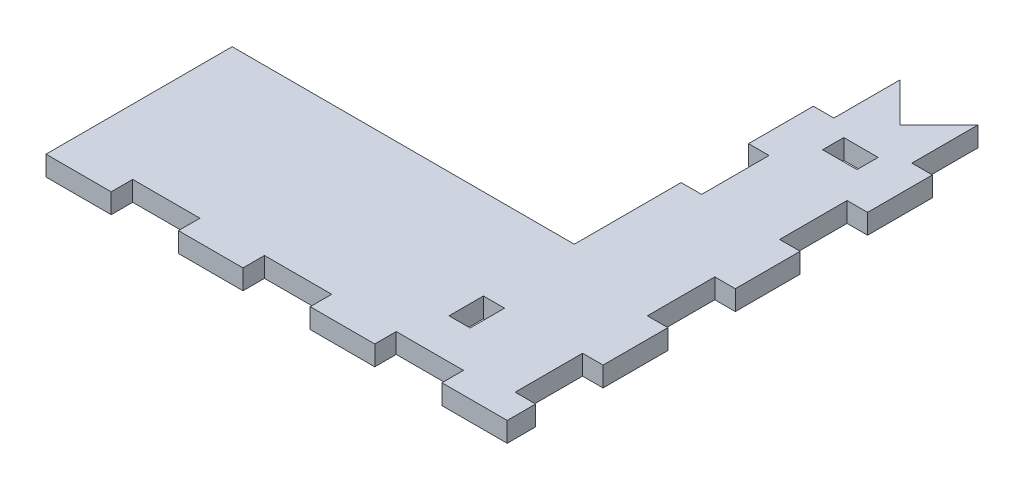
SolidWorks part; units mm, degrees
ref_plane "Front Plane" through (0, 0, 0) normal (0, 0, 1) x (1, 0, 0)
ref_plane "Top Plane" through (0, 0, 0) normal (0, 1, 0) x (1, 0, 0)
ref_plane "Right Plane" through (0, 0, 0) normal (1, 0, 0) x (0, 0, -1)
sketch "Sketch1" plane through (0, 0, 0) normal (0, 1, 0) x (1, 0, 0)
  line L0 (0, 0) -> (0, 75) construction
  line L1 (-34.8722, 75) -> (34.8722, 75) construction
  line L2 (-34.8722, 75) -> (-34.8722, 0) construction
  line L3 (-34.8722, 0) -> (34.8722, 0)
  line L4 (34.8722, 75) -> (34.8722, 0)
  line L5 (34.8722, 0) -> (34.8722, 75) construction
  line L6 (34.8722, 75) -> (16.8722, 75)
  line L7 (16.8722, 75) -> (16.8722, 28.75)
  line L8 (16.8722, 28.75) -> (-34.8722, 28.75)
  line L9 (-34.8722, 28.75) -> (-34.8722, 0)
  line L10 (24.9087, 3.75) -> (24.9087, 10.75) construction
  line L12 (19.8722, 75) -> (19.8722, 0) construction
  line L13 (31.8722, 75) -> (31.8722, 0) construction
  line L14 (31.8722, 37.5) -> (34.8722, 37.5) construction
  line L15 (19.8722, 37.5) -> (16.8722, 37.5) construction
  line L16 (31.8722, 75) -> (25.8722, 69) construction
  line L17 (25.8722, 69) -> (19.8722, 75) construction
  line L18 (25.8722, 75) -> (25.8722, 69) construction
  line L19 (25.8722, 69) -> (31.8722, 69) construction
  line L20 (34.8722, 60) -> (16.8722, 60) construction
  line L21 (16.8722, 63) -> (34.8722, 63) construction
  line L22 (25.8722, 63) -> (25.8722, 60) construction
  line L23 (-34.8722, 3) -> (34.8722, 3) construction
  line L24 (-34.8722, 0) -> (-34.8722, -0.75) construction
  line L25 (-34.8722, -0.75) -> (34.8722, -0.75) construction
  line L26 (34.8722, -0.75) -> (34.8722, 0) construction
  line L27 (-3, 0) -> (-3, 3) construction
  line L28 (-3, 1.5) -> (0, 1.5) construction
  line L29 (-34.8722, 3.75) -> (34.8722, 3.75) construction
  line L30 (-3, 3) -> (-3, 3.75) construction
  line L31 (-3, 0) -> (-3, -0.75) construction
  line L34 (-24.9087, 0) -> (-24.9087, 3.75) construction
  line L39 (-14.9452, 0) -> (-14.9452, 3.75) construction
  line L40 (-4.9817, 0) -> (-4.9817, 3.75) construction
  line L41 (4.9817, 0) -> (4.9817, 3.75) construction
  line L42 (14.9452, 0) -> (14.9452, 3.75) construction
  line L43 (24.9087, 0) -> (24.9087, 3.75) construction
  line L44 (34.8722, 0.5) -> (-34.8722, 0.5) construction
  line L45 (24.9087, 10.75) -> (-24.9087, 10.75) construction
  line L46 (-24.9087, 10.75) -> (-24.9087, 3.75) construction
  line L47 (16.8722, 28.75) -> (16.8722, 10.75) construction
  line L48 (16.8722, 28.75) -> (34.8722, 28.75) construction
  dimension "D1" = 12
  dimension "D2" = 0.75
  dimension "D3" = 0.5
  dimension "D4" = 7
extrude "Boss-Extrude1" add sketch "Sketch1" against normal up to vertex (3 mm away)
sketch "Sketch2" plane through (0, 0, 0) normal (0, 1, 0) x (1, 0, 0)
  line L0 (-34.8722, 0) -> (34.8722, 0) construction
  line L2 (28.3722, 60) -> (23.3722, 60)
  line L3 (34.8722, 75) -> (34.8722, 0) construction
  line L4 (34.8722, 75) -> (16.8722, 75) construction
  line L5 (16.8722, 75) -> (16.8722, 28.75) construction
  line L6 (16.8722, 28.75) -> (-34.8722, 28.75) construction
  line L7 (-34.8722, 28.75) -> (-34.8722, 0) construction
  line L8 (-34.8722, 0) -> (34.8722, 0)
  line L9 (34.8722, 75) -> (34.8722, 0) construction
  line L10 (34.8722, 75) -> (16.8722, 75) construction
  line L11 (16.8722, 75) -> (16.8722, 28.75) construction
  line L12 (16.8722, 28.75) -> (-34.8722, 28.75) construction
  line L13 (-34.8722, 28.75) -> (-34.8722, 0) construction
  line L14 (31.8722, 75) -> (31.8722, 0) construction
  line L15 (19.8722, 0) -> (19.8722, 75) construction
  line L16 (34.8722, 3.75) -> (-34.8722, 3.75) construction
  line L17 (34.8722, 60) -> (16.8722, 60) construction
  line L18 (34.8722, 63) -> (16.8722, 63) construction
  line L19 (16.8722, 63) -> (34.8722, 63) construction
  line L20 (34.8722, 60) -> (16.8722, 60) construction
  line L21 (31.8722, 75) -> (31.8722, 0) construction
  line L22 (-34.8722, 3.75) -> (34.8722, 3.75) construction
  line L23 (25.8722, 60) -> (25.8722, 3.75) construction
  line L24 (34.8722, 0) -> (34.8722, 0.5)
  line L25 (25.8722, 60) -> (25.8722, 63) construction
  line L26 (28.3722, 60) -> (28.3722, 63)
  line L27 (28.3722, 63) -> (23.3722, 63)
  line L28 (23.3722, 60) -> (23.3722, 63)
  line L29 (31.8722, 65) -> (34.8722, 65)
  line L30 (33.3722, 65) -> (33.3722, 75) construction
  line L31 (33.3722, 65) -> (33.3722, 55) construction
  line L32 (34.8722, 55) -> (31.8722, 55)
  line L33 (31.8722, 45) -> (34.8722, 45)
  line L34 (33.3722, 55) -> (33.3722, 45) construction
  line L37 (33.3722, 45) -> (33.3722, 35) construction
  line L38 (34.8722, 35) -> (31.8722, 35)
  line L39 (34.8722, 25) -> (31.8722, 25)
  line L40 (33.3722, 25) -> (33.3722, 35) construction
  line L41 (34.8722, 15) -> (31.8722, 15)
  line L42 (34.8722, 5) -> (31.8722, 5)
  line L43 (33.3722, 5) -> (33.3722, 15) construction
  line L44 (33.3722, 15) -> (33.3722, 25) construction
  line L47 (34.8722, 0.5) -> (24.9087, 0.5)
  line L48 (0, 0) -> (0, 75) construction
  line L49 (0, 0) -> (0, 75) construction
  line L54 (24.9087, 0) -> (24.9087, 3.75) construction
  line L55 (24.9087, 0.5) -> (24.9087, 3.75)
  line L108 (31.8722, 25) -> (31.8722, 35)
  line L109 (34.8722, 25) -> (34.8722, 35)
  line L110 (31.8722, 45) -> (31.8722, 55)
  line L111 (34.8722, 55) -> (34.8722, 45)
  line L112 (34.8722, 65) -> (34.8722, 75)
  line L113 (34.8722, 75) -> (31.8722, 75)
  line L114 (31.8722, 75) -> (31.8722, 65)
  line L115 (16.8722, 25) -> (19.8722, 25) construction
  line L116 (16.8722, 25) -> (16.8722, 35) construction
  line L117 (16.8722, 35) -> (19.8722, 35) construction
  line L118 (19.8722, 25) -> (19.8722, 35) construction
  line L119 (19.8722, 45) -> (16.8722, 45)
  line L120 (16.8722, 55) -> (16.8722, 45)
  line L121 (16.8722, 55) -> (19.8722, 55)
  line L122 (19.8722, 45) -> (19.8722, 55)
  line L123 (16.8722, 75) -> (19.8722, 75)
  line L124 (16.8722, 65) -> (16.8722, 75)
  line L125 (19.8722, 65) -> (16.8722, 65)
  line L126 (19.8722, 75) -> (19.8722, 65)
  line L133 (31.8722, 5) -> (31.8722, 15)
  line L134 (34.8722, 15) -> (34.8722, 5)
  line L135 (24.9087, 3.75) -> (14.9452, 3.75)
  line L136 (14.9452, 3.75) -> (14.9452, 0.5)
  line L137 (14.9452, 0.5) -> (4.9817, 0.5)
  line L138 (4.9817, 0.5) -> (4.9817, 3.75)
  line L139 (4.9817, 3.75) -> (-4.9817, 3.75)
  line L140 (-4.9817, 3.75) -> (-4.9817, 0.5)
  line L141 (-4.9817, 0.5) -> (-14.9452, 0.5)
  line L142 (-14.9452, 0.5) -> (-14.9452, 3.75)
  line L143 (-14.9452, 3.75) -> (-24.9087, 3.75)
  line L144 (-24.9087, 3.75) -> (-24.9087, 0.5)
  line L145 (-24.9087, 0.5) -> (-34.8722, 0.5)
  line L146 (-34.8722, 0.5) -> (-34.8722, 0)
  line L147 (-14.9452, 0) -> (-14.9452, 3.75) construction
  line L148 (34.8722, 0.5) -> (-34.8722, 0.5) construction
  line L149 (4.9817, 0) -> (4.9817, 3.75) construction
  line L150 (14.9452, 0) -> (14.9452, 3.75) construction
  line L152 (19.8722, 15) -> (16.8722, 15)
  line L153 (19.8722, 15) -> (19.8722, 10)
  line L154 (19.8722, 10) -> (16.8722, 10)
  line L155 (16.8722, 15) -> (16.8722, 10)
  dimension "D1" = 5
  dimension "D2" = 10
  dimension "D3" = 5
sketch "Sketch8" plane through (0, 0, 0) normal (0, 1, 0) x (1, 0, 0)
  line L45 (34.9722, 55.1) -> (31.7722, 55.1)
  line L46 (31.7722, 55.1) -> (31.7722, 44.9)
  line L47 (31.7722, 44.9) -> (34.9722, 44.9)
  line L48 (34.9722, 44.9) -> (34.9722, 55.1)
  line L49 (34.8722, 55) -> (31.8722, 55)
  line L50 (31.8722, 55) -> (31.8722, 45)
  line L51 (31.8722, 45) -> (34.8722, 45)
  line L52 (34.8722, 45) -> (34.8722, 55)
  line L53 (34.8722, 55) -> (31.8722, 55) construction
  line L54 (31.8722, 55) -> (31.8722, 45) construction
  line L55 (31.8722, 45) -> (34.8722, 45) construction
  line L56 (34.8722, 45) -> (34.8722, 55) construction
  line L57 (31.8722, 65) -> (34.8722, 65)
  line L58 (34.8722, 65) -> (34.8722, 75)
  line L59 (34.8722, 75) -> (31.8722, 75)
  line L60 (31.8722, 75) -> (31.8722, 65)
  line L61 (31.8722, 65) -> (34.8722, 65) construction
  line L62 (34.8722, 65) -> (34.8722, 75) construction
  line L63 (34.8722, 75) -> (31.8722, 75) construction
  line L64 (31.8722, 75) -> (31.8722, 65) construction
  line L65 (23.3722, 60) -> (28.3722, 60)
  line L66 (28.3722, 60) -> (28.3722, 63)
  line L67 (28.3722, 63) -> (23.3722, 63)
  line L68 (23.3722, 63) -> (23.3722, 60)
  line L69 (23.3722, 60) -> (28.3722, 60) construction
  line L70 (28.3722, 60) -> (28.3722, 63) construction
  line L71 (28.3722, 63) -> (23.3722, 63) construction
  line L72 (23.3722, 63) -> (23.3722, 60) construction
  line L73 (34.8722, 15) -> (31.8722, 15)
  line L74 (31.8722, 15) -> (31.8722, 5)
  line L75 (31.8722, 5) -> (34.8722, 5)
  line L76 (34.8722, 5) -> (34.8722, 15)
  line L77 (34.8722, 15) -> (31.8722, 15) construction
  line L78 (31.8722, 15) -> (31.8722, 5) construction
  line L79 (31.8722, 5) -> (34.8722, 5) construction
  line L80 (34.8722, 5) -> (34.8722, 15) construction
  line L81 (31.8722, 35) -> (31.8722, 25)
  line L82 (31.8722, 25) -> (34.8722, 25)
  line L83 (34.8722, 25) -> (34.8722, 35)
  line L84 (34.8722, 35) -> (31.8722, 35)
  line L85 (31.8722, 35) -> (31.8722, 25) construction
  line L86 (31.8722, 25) -> (34.8722, 25) construction
  line L87 (34.8722, 25) -> (34.8722, 35) construction
  line L88 (34.8722, 35) -> (31.8722, 35) construction
  line L89 (19.8722, 15) -> (16.8722, 15) construction
  line L90 (16.8722, 15) -> (16.8722, 10) construction
  line L91 (19.8722, 10) -> (16.8722, 10) construction
  line L92 (19.8722, 15) -> (19.8722, 10) construction
  line L93 (19.8722, 15) -> (16.8722, 15) construction
  line L94 (16.8722, 15) -> (16.8722, 10) construction
  line L95 (19.8722, 10) -> (16.8722, 10) construction
  line L96 (19.8722, 15) -> (19.8722, 10) construction
  line L97 (16.8722, 65) -> (19.8722, 65)
  line L98 (19.8722, 65) -> (19.8722, 75)
  line L99 (19.8722, 75) -> (16.8722, 75)
  line L100 (16.8722, 75) -> (16.8722, 65)
  line L101 (16.8722, 65) -> (19.8722, 65) construction
  line L102 (19.8722, 65) -> (19.8722, 75) construction
  line L103 (19.8722, 75) -> (16.8722, 75) construction
  line L104 (16.8722, 75) -> (16.8722, 65) construction
  line L105 (16.8722, 55) -> (16.8722, 45)
  line L106 (19.8722, 55) -> (16.8722, 55)
  line L107 (19.8722, 45) -> (19.8722, 55)
  line L108 (16.8722, 45) -> (19.8722, 45)
  line L109 (-34.8722, 0.5) -> (-34.8722, 0)
  line L110 (-34.8722, 0) -> (34.8722, 0)
  line L111 (34.8722, 0) -> (34.8722, 0.5)
  line L112 (34.8722, 0.5) -> (24.9087, 0.5)
  line L113 (24.9087, 0.5) -> (24.9087, 3.75)
  line L114 (24.9087, 3.75) -> (14.9452, 3.75)
  line L115 (14.9452, 3.75) -> (14.9452, 0.5)
  line L116 (14.9452, 0.5) -> (4.9817, 0.5)
  line L117 (4.9817, 0.5) -> (4.9817, 3.75)
  line L118 (4.9817, 3.75) -> (-4.9817, 3.75)
  line L119 (-4.9817, 3.75) -> (-4.9817, 0.5)
  line L120 (-4.9817, 0.5) -> (-14.9452, 0.5)
  line L121 (-14.9452, 0.5) -> (-14.9452, 3.75)
  line L122 (-14.9452, 3.75) -> (-24.9087, 3.75)
  line L123 (-24.9087, 3.75) -> (-24.9087, 0.5)
  line L124 (-24.9087, 0.5) -> (-34.8722, 0.5)
  line L125 (-34.8722, 0.5) -> (-34.8722, 0) construction
  line L126 (-34.8722, 0) -> (34.8722, 0) construction
  line L127 (34.8722, 0) -> (34.8722, 0.5) construction
  line L128 (34.8722, 0.5) -> (24.9087, 0.5) construction
  line L129 (24.9087, 0.5) -> (24.9087, 3.75) construction
  line L130 (24.9087, 3.75) -> (14.9452, 3.75) construction
  line L131 (14.9452, 3.75) -> (14.9452, 0.5) construction
  line L132 (14.9452, 0.5) -> (4.9817, 0.5) construction
  line L133 (4.9817, 0.5) -> (4.9817, 3.75) construction
  line L134 (4.9817, 3.75) -> (-4.9817, 3.75) construction
  line L135 (-4.9817, 3.75) -> (-4.9817, 0.5) construction
  line L136 (-4.9817, 0.5) -> (-14.9452, 0.5) construction
  line L137 (-14.9452, 0.5) -> (-14.9452, 3.75) construction
  line L138 (-14.9452, 3.75) -> (-24.9087, 3.75) construction
  line L139 (-24.9087, 3.75) -> (-24.9087, 0.5) construction
  line L140 (-24.9087, 0.5) -> (-34.8722, 0.5) construction
  line L142 (16.8722, 55) -> (16.8722, 45) construction
  line L143 (19.8722, 55) -> (16.8722, 55) construction
  line L144 (19.8722, 45) -> (19.8722, 55) construction
  line L146 (16.8722, 45) -> (19.8722, 45) construction
  line L147 (31.7722, 64.9) -> (34.9722, 64.9)
  line L148 (34.9722, 64.9) -> (34.9722, 75.1)
  line L149 (34.9722, 75.1) -> (31.7722, 75.1)
  line L150 (31.7722, 75.1) -> (31.7722, 64.9)
  line L151 (23.2722, 59.9) -> (28.4722, 59.9)
  line L152 (28.4722, 59.9) -> (28.4722, 63.1)
  line L153 (28.4722, 63.1) -> (23.2722, 63.1)
  line L154 (23.2722, 63.1) -> (23.2722, 59.9)
  line L155 (34.9722, 15.1) -> (31.7722, 15.1)
  line L156 (31.7722, 15.1) -> (31.7722, 4.9)
  line L157 (31.7722, 4.9) -> (34.9722, 4.9)
  line L158 (34.9722, 4.9) -> (34.9722, 15.1)
  line L159 (31.7722, 35.1) -> (31.7722, 24.9)
  line L160 (31.7722, 24.9) -> (34.9722, 24.9)
  line L161 (34.9722, 24.9) -> (34.9722, 35.1)
  line L162 (34.9722, 35.1) -> (31.7722, 35.1)
  line L163 (19.9722, 15.1) -> (16.7722, 15.1)
  line L164 (16.7722, 15.1) -> (16.7722, 9.9)
  line L165 (19.9722, 9.9) -> (16.7722, 9.9)
  line L166 (19.9722, 15.1) -> (19.9722, 9.9)
  line L167 (16.7722, 64.9) -> (19.9722, 64.9)
  line L168 (19.9722, 64.9) -> (19.9722, 75.1)
  line L169 (19.9722, 75.1) -> (16.7722, 75.1)
  line L170 (16.7722, 75.1) -> (16.7722, 64.9)
  line L171 (-34.9722, 0.6) -> (-34.9722, -0.1)
  line L172 (-34.9722, -0.1) -> (34.9722, -0.1)
  line L173 (34.9722, -0.1) -> (34.9722, 0.6)
  line L174 (34.9722, 0.6) -> (25.0087, 0.6)
  line L175 (25.0087, 0.6) -> (25.0087, 3.85)
  line L176 (25.0087, 3.85) -> (14.8452, 3.85)
  line L177 (14.8452, 3.85) -> (14.8452, 0.6)
  line L178 (14.8452, 0.6) -> (5.0817, 0.6)
  line L179 (5.0817, 0.6) -> (5.0817, 3.85)
  line L180 (5.0817, 3.85) -> (-5.0817, 3.85)
  line L181 (-5.0817, 3.85) -> (-5.0817, 0.6)
  line L182 (-5.0817, 0.6) -> (-14.8452, 0.6)
  line L183 (-14.8452, 0.6) -> (-14.8452, 3.85)
  line L184 (-14.8452, 3.85) -> (-25.0087, 3.85)
  line L185 (-25.0087, 3.85) -> (-25.0087, 0.6)
  line L186 (-25.0087, 0.6) -> (-34.9722, 0.6)
  line L187 (16.7722, 55.1) -> (16.7722, 44.9)
  line L188 (16.7722, 44.9) -> (19.9722, 44.9)
  line L189 (19.9722, 44.9) -> (19.9722, 55.1)
  line L190 (19.9722, 55.1) -> (16.7722, 55.1)
  dimension "D1" = 0
  dimension "D2" = 0
  dimension "D3" = 0
  dimension "D4" = 0
  dimension "D5" = 0
  dimension "D6" = 0.1
  dimension "D7" = 0
  dimension "D8" = 0
  dimension "D9" = 0
  dimension "D10" = 0.1
extrude "Cut-Extrude4" cut sketch "Sketch8" against normal through all
sketch "Sketch5" plane through (0, 0, 0) normal (0, 1, 0) x (1, 0, 0)
  line L0 (31.8722, 75) -> (25.8722, 69)
  line L1 (25.8722, 69) -> (19.8722, 75)
  line L2 (19.8722, 75) -> (31.8722, 75)
extrude "Cut-Extrude2" cut sketch "Sketch5" against normal through all
